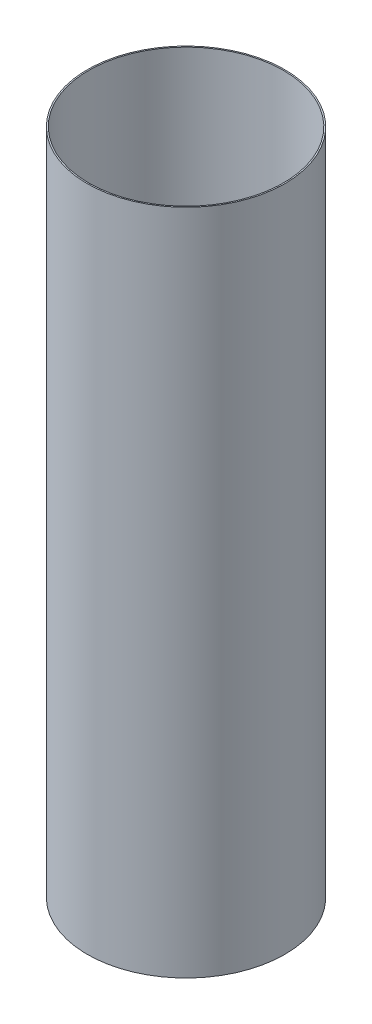
SolidWorks part; units mm, degrees
ref_plane "Ebene vorne" through (0, 0, 0) normal (0, 0, 1) x (1, 0, 0)
ref_plane "Ebene oben" through (0, 0, 0) normal (0, 1, 0) x (1, 0, 0)
ref_plane "Ebene rechts" through (0, 0, 0) normal (1, 0, 0) x (0, 0, -1)
sketch "Sketch1" plane through (0, 0, 0) normal (0, 1, 0) x (1, 0, 0)
  circle A0 centre (0, 0) radius 73
  dimension "D1" = 146
extrude "Extrude-Thin1" add sketch "Sketch1" along normal mid plane 500 thin
